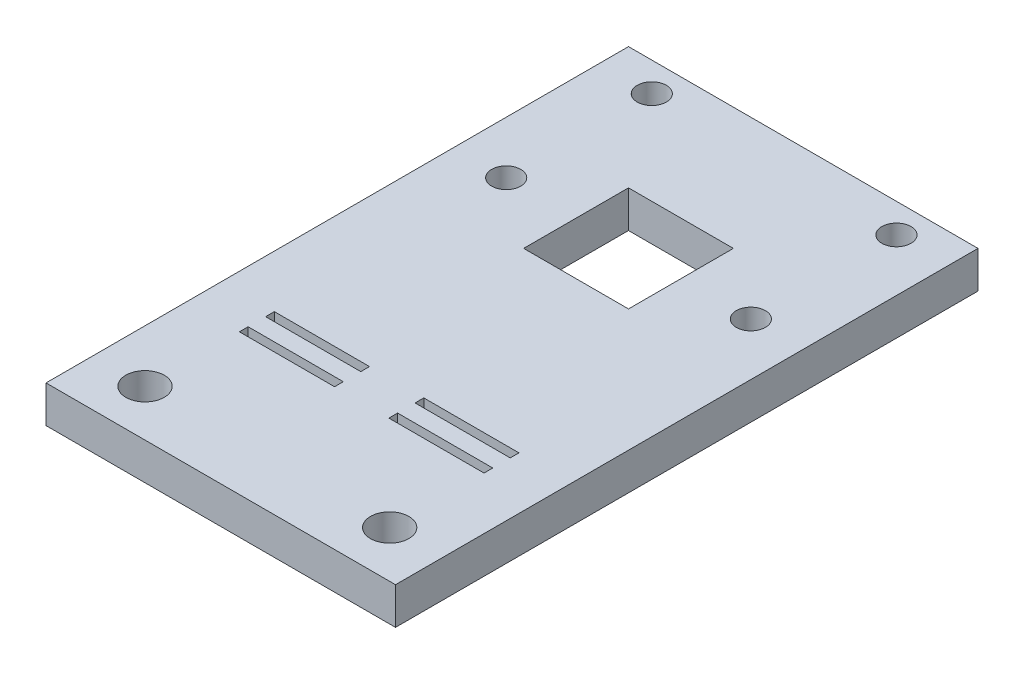
SolidWorks part; units mm, degrees
ref_plane "Front Plane" through (0, 0, 0) normal (0, 0, 1) x (1, 0, 0)
ref_plane "Top Plane" through (0, 0, 0) normal (0, 1, 0) x (1, 0, 0)
ref_plane "Right Plane" through (0, 0, 0) normal (1, 0, 0) x (0, 0, -1)
sketch "Sketch1" plane through (0, 0, 0) normal (0, 1, 0) x (1, 0, 0)
  line L0 (0, 25) -> (0, -25) construction
  line L1 (-15, 25) -> (15, 25)
  line L2 (-15, 25) -> (-15, -25)
  line L3 (-15, -25) -> (15, -25)
  line L4 (15, 25) -> (15, -25)
  line L5 (-15, 25) -> (15, -25) construction
  line L6 (-15, -25) -> (15, 25) construction
  line L7 (-10.5, 10) -> (-4.5, 10)
  line L12 (-10.5, 22.5) -> (10.5, 22.5) construction
  line L13 (-10.5, 22.5) -> (-10.5, 10) construction
  line L14 (-10.5, 10) -> (10.5, 10) construction
  line L15 (10.5, 22.5) -> (10.5, 10) construction
  line L16 (-10.5, 22.5) -> (10.5, 10) construction
  line L17 (-10.5, 10) -> (10.5, 22.5) construction
  line L19 (10.5, 10) -> (4.5, 10)
  line L25 (2.33, -10.6505) -> (2.33, -9.9005)
  line L26 (-10.5, -16.9005) -> (10.5, -16.9005) construction
  line L27 (-10.5, -16.9005) -> (-10.5, -21) construction
  line L28 (-10.5, -21) -> (10.5, -21) construction
  line L29 (10.5, -16.9005) -> (10.5, -21) construction
  line L30 (-10.5, -16.9005) -> (10.5, -21) construction
  line L31 (-10.5, -21) -> (10.5, -16.9005) construction
  line L32 (-10.5, -12.9005) -> (-2.33, -12.9005)
  line L33 (-10.5, -12.9005) -> (-10.5, -12.1505)
  line L34 (-10.5, -12.1505) -> (-2.33, -12.1505)
  line L35 (-2.33, -12.9005) -> (-2.33, -12.1505)
  line L36 (-10.5, -10.6505) -> (-2.33, -10.6505)
  line L37 (-10.5, -10.6505) -> (-10.5, -9.9005)
  line L38 (-10.5, -9.9005) -> (-2.33, -9.9005)
  line L39 (-2.33, -10.6505) -> (-2.33, -9.9005)
  line L40 (10.5, -9.9005) -> (2.33, -9.9005)
  line L41 (10.5, -10.6505) -> (10.5, -9.9005)
  line L42 (10.5, -10.6505) -> (2.33, -10.6505)
  line L43 (2.33, -12.9005) -> (2.33, -12.1505)
  line L44 (10.5, -12.1505) -> (2.33, -12.1505)
  line L45 (10.5, -12.9005) -> (10.5, -12.1505)
  line L46 (10.5, -12.9005) -> (2.33, -12.9005)
  line L48 (-4.5, 14.5) -> (4.5, 14.5)
  line L49 (-4.5, 14.5) -> (-4.5, 5.5)
  line L50 (-4.5, 5.5) -> (4.5, 5.5)
  line L51 (4.5, 14.5) -> (4.5, 5.5)
  circle A0 centre (-10.5, 22.5) radius 1.25
  circle A1 centre (10.5, 22.5) radius 1.25
  circle A2 centre (10.5, 10) radius 1.25
  circle A3 centre (-10.5, 10) radius 1.25
  circle A6 centre (-10.5, -21) radius 1.65
  circle A7 centre (10.5, -21) radius 1.65
  point P0 (0, 0)
  point P8 (0, 16.25)
  point P17 (0, 37.4889)
  point P18 (0, -18.9503)
  dimension "D6" = 2.5
  dimension "D10" = 21
  dimension "D11" = 4
  dimension "D12" = 3.3
  dimension "D1" = 12.5
  dimension "D2" = 21
  dimension "D3" = 2.5
  dimension "D4" = 50
  dimension "D5" = 4.5
  dimension "D7" = 6
  dimension "D8" = 6
  dimension "D9" = 9
  dimension "D13" = 4
  dimension "D14" = 0.75
  dimension "D15" = 1.5
  dimension "D16" = 4.5
extrude "Boss-Extrude1" add sketch "Sketch1" along normal blind 3.175
